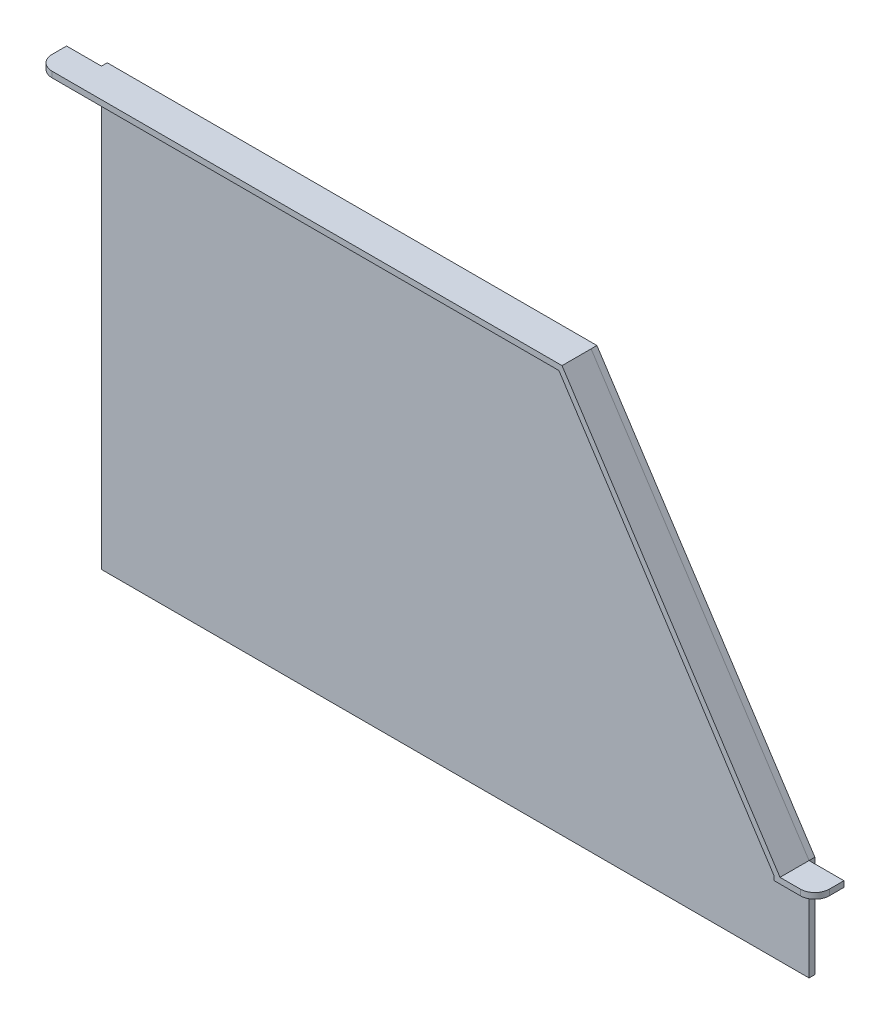
SolidWorks part; units mm, degrees
material "6061-T6 (SS)"
ref_plane "Front Plane" through (0, 0, 0) normal (0, 0, 1) x (1, 0, 0)
ref_plane "Top Plane" through (0, 0, 0) normal (0, 1, 0) x (1, 0, 0)
ref_plane "Right Plane" through (0, 0, 0) normal (1, 0, 0) x (0, 0, -1)
sketch "Sketch1" plane through (0, 0, 0) normal (0, 0, 1) x (1, 0, 0)
  line L0 (0, 0) -> (0, 300)
  line L1 (0, 300) -> (337, 300)
  line L2 (337, 300) -> (487, 70)
  line L3 (487, 70) -> (487, 0)
  line L4 (487, 0) -> (0, 0)
  dimension "D1" = 300
  dimension "D2" = 70
  dimension "D3" = 337
  dimension "D4" = 487
extrude "Boss-Extrude1" add sketch "Sketch1" along normal blind 4
sketch "Sketch7" plane through (0, 0, 4) normal (0, 0, 1) x (1, 0, 0)
  line L1 (0, 300) -> (336.996, 300)
  line L2 (0, 300) -> (0, 296)
  line L3 (0, 296) -> (336.996, 296)
  line L4 (336.996, 300) -> (336.996, 296)
  dimension "D1" = 4
extrude "Boss-Extrude2" add sketch "Sketch7" along normal blind 20
sketch "Sketch8" plane through (0, 0, 4) normal (0, 0, 1) x (1, 0, 0)
  line L0 (336.996, 300) -> (487, 70)
  line L1 (487, 70) -> (483.6496, 67.8149)
  line L2 (483.6496, 67.8149) -> (333.6456, 297.8149)
  line L3 (333.6456, 297.8149) -> (336.996, 300)
  dimension "D1" = 4
extrude "Boss-Extrude3" add sketch "Sketch8" along normal blind 20
sketch "Sketch9" plane through (0, 0, 4) normal (0, 0, 1) x (1, 0, 0)
  line L1 (487, 70) -> (483, 70)
  line L2 (487, 70) -> (487, 66)
  line L3 (487, 66) -> (483, 66)
  line L4 (483, 70) -> (483, 66)
  dimension "D1" = 4
  dimension "D2" = 4
extrude "Boss-Extrude4" add sketch "Sketch9" along normal blind 20
sketch "Sketch10" plane through (487, 0, 0) normal (1, 0, 0) x (0, 0, -1)
  line L5 (-4, 70) -> (-24, 70)
  line L6 (-4, 70) -> (-4, 66)
  line L7 (-4, 66) -> (-24, 66)
  line L8 (-24, 70) -> (-24, 66)
extrude "Boss-Extrude5" add sketch "Sketch10" along normal blind 24
sketch "Sketch12" plane through (0, 0, 0) normal (-1, 0, 0) x (0, 0, 1)
  line L6 (24, 300) -> (4, 300)
  line L7 (24, 300) -> (24, 296)
  line L8 (24, 296) -> (4, 296)
  line L9 (4, 300) -> (4, 296)
extrude "Boss-Extrude6" add sketch "Sketch12" along normal blind 24
fillet "Fillet1" radius 10 2 edges at (511, 68, 24) (-24, 298, 24)
